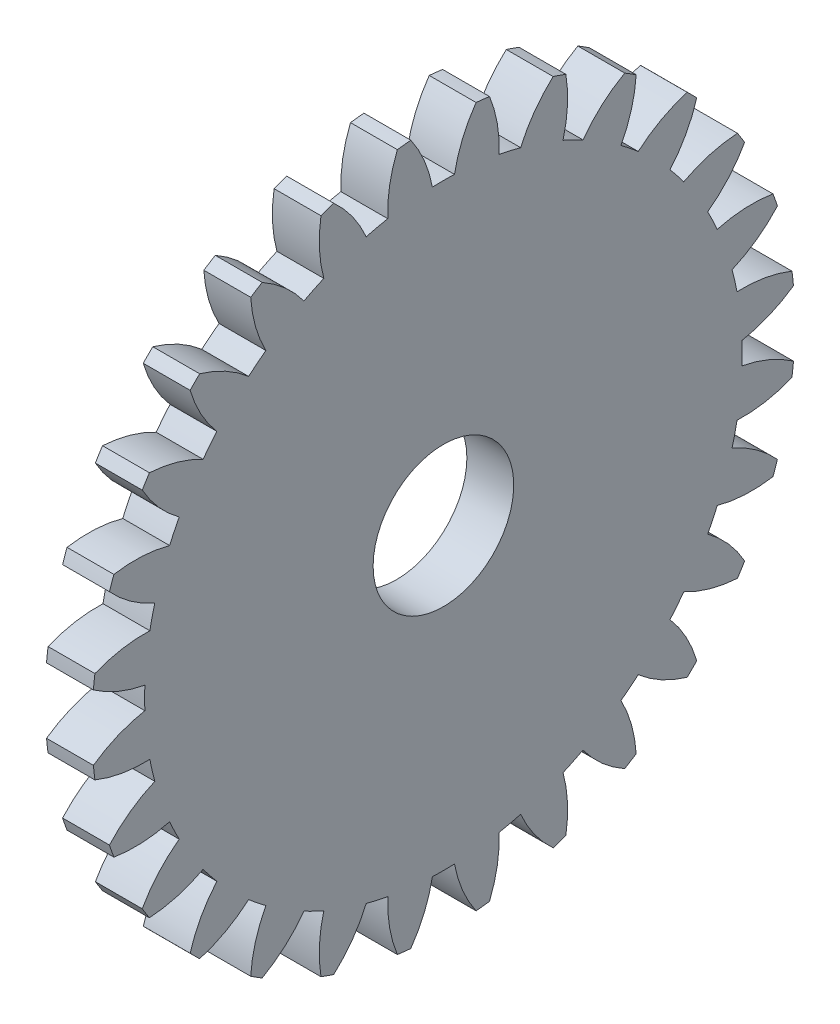
SolidWorks part; units mm, degrees
ref_plane "Plane1" through (0, 0, 0) normal (0, 0, 1) x (1, 0, 0)
ref_plane "Plane2" through (0, 0, 0) normal (0, 1, 0) x (1, 0, 0)
ref_plane "Plane3" through (0, 0, 0) normal (1, 0, 0) x (0, 0, -1)
sketch "HoldingSke" plane through (0, 0, 0) normal (0, 1, 0) x (1, 0, 0)
  line L0 (0, 0) -> (0.8829, -0.4695)
  line L1 (-15, 0) -> (100, 0) construction
  line L2 (0, 0) -> (-2.1039, 2.3779)
  line L3 (0, 0) -> (-11.863, 4.5341)
  line L4 (0, 0) -> (7.6251, 4.0544)
  line L5 (0, 0) -> (-46.8476, -17.4728)
  line L6 (0, 0) -> (-1.6579, -1.1186)
  line L7 (-2.1039, 2.3779) -> (8.6586, 51.2059)
  line L8 (-76.2, 54.61) -> (-75.2, 54.61)
  line L9 (-71.009, 38.7566) -> (-53.1078, 45.2721)
  line L10 (-76.2, 71.12) -> (104.1128, 71.12)
  line L11 (0, 0) -> (-2, 0)
  line L12 (-76.2, 101.6) -> (-76.162, 101.6)
  line L13 (24.9733, 27.94) -> (52.9518, 28.4284)
  line L14 (24.9733, 27.94) -> (24.9743, 27.94)
  line L15 (24.9733, 27.94) -> (100.4006, 29.5858)
  line L16 (-63.627, -1) -> (-12.827, -1)
  circle A0 centre (0, 0) radius 3
  circle A1 centre (0, 0) radius 12.749
  circle A2 centre (0, 0) radius 37.5
  circle A3 centre (0, 0) radius 3
  dimension "MHD" = 25.498
  dimension "Hub_dia" = 75
  dimension "Bore" = 6
  dimension "MBD" = 6
  dimension "Num_teeth" = 28
  dimension "Pitch_radius" = 180.3128
  dimension "Pitch" = 1
  dimension "Width" = 2
  dimension "Overall_len" = 50
  dimension "Show_teeth" = 28
  dimension "Thickness" = 2
  dimension "OAL" = 50.0001
  dimension "T_dim" = 1
  dimension "Ap" = 20
  dimension "H" = 19.05
  dimension "Backlash" = 0.038
  dimension "Addendum_fac" = 1
  dimension "Dedendum_fac" = 1.25
  dimension "Clearance_fac" = 0.25
  dimension "Dedendum_add" = 0.001
  dimension "Module" = 1
sketch "BasProSke" plane through (0, 0, 0) normal (0, 1, 0) x (1, 0, 0)
  line L0 (-10, 0) -> (60, 0) construction
  line L1 (0, 0) -> (0, 15)
  line L2 (0, 0) -> (2, 0)
  line L3 (2, 0) -> (2, 15)
  line L4 (2, 15) -> (0, 15)
  dimension "Diameter" = 30
  dimension "Thickness" = 2
revolve "Base-Revolve" add sketch "BasProSke" angle 360 about L0
sketch "TooCutSke" plane through (0, 0, 0) normal (1, 0, 0) x (0, 0, -1)
  line L1 (0, 0) -> (0, 107) construction
  line L2 (0, 0) -> (-0.8515, 13.9741) construction
  line L3 (0, 0) -> (-3.1309, 27.7873) construction
  line L4 (-0.8515, 13.9741) -> (-1.5654, 13.8936) construction
  arc A0 (0.4713, 12.7403) -> (-0.4713, 12.7403) centre (0, 0) ccw
  arc A1 (1.4098, 14.9591) -> (-1.4098, 14.9591) centre (0, 0) ccw
  circle A2 centre (0, 0) radius 14 construction
  circle A3 centre (0, 0) radius 13.1557 construction
  arc A4 (-0.4713, 12.7403) -> (-1.4098, 14.9591) centre (-5.9775, 11.7193) ccw
  arc A5 (1.4098, 14.9591) -> (0.4713, 12.7403) centre (5.9775, 11.7193) ccw
  dimension "Root_dia" = 25.498
  dimension "Overcut_dia" = 30.0508
  dimension "Pitch_dia" = 28
  dimension "Base_dia" = 26.3114
  dimension "Flank_rad" = 5.6
  dimension "Half_ang" = 6.429
  dimension "Half_CT" = 0.7185
extrude "ToothCut" cut sketch "TooCutSke" along normal through all
fillet "Breaks" [suppressed] radius 0.02
fillet "RootFillets" [suppressed] radius 0.251
pattern_circular "TeethCuts" count 28 every 12.857 about axis through (-10, 0, 0) along (1, 0, 0) of "ToothCut", "RootFillets", "Breaks"
sketch "HubNeaOneSke" plane through (0, 0, 0) normal (-1, 0, 0) x (0, 0, 1)
  circle A0 centre (0, 0) radius 12.749
  dimension "Diameter" = 25.498
extrude "HubNearOne" [suppressed] add sketch "HubNeaOneSke" along normal blind 48.0001
sketch "HubNeaBotSke" plane through (0, 0, 0) normal (-1, 0, 0) x (0, 0, 1)
  circle A0 centre (0, 0) radius 12.749
  dimension "Diameter" = 25.498
extrude "HubNearBoth" [suppressed] add sketch "HubNeaBotSke" along normal blind 24
ref_plane "FarPln" through (2, 0, 0) normal (1, 0, 0) x (0, 0, -1)
sketch "HubFarSke" plane through (2, 0, 0) normal (1, 0, 0) x (0, 0, -1)
  circle A0 centre (0, 0) radius 12.749
  dimension "Diameter" = 25.498
extrude "HubFar" [suppressed] add sketch "HubFarSke" along normal blind 24
sketch "BorSke" plane through (0, 0, 0) normal (1, 0, 0) x (0, 0, -1)
  circle A0 centre (0, 0) radius 3
  dimension "Diameter" = 6
extrude "Bore" cut sketch "BorSke" along normal mid plane 100.0001
sketch "KeySke" plane through (0, 0, 0) normal (1, 0, 0) x (0, 0, -1)
  line L0 (-1, 0) -> (-1, 4)
  line L1 (-1, 4) -> (1, 4)
  line L2 (1, 4) -> (1, 0)
  line L3 (0, 0) -> (0, 34) construction
  line L4 (-1, 0) -> (1, 0)
  dimension "Offset" = 4
  dimension "Width" = 2
extrude "Keyway" [suppressed] cut sketch "KeySke" along normal mid plane 100.0001
pattern_circular "Keyway2" [suppressed] count 2 every 90 about axis through (-10, 0, 0) along (1, 0, 0)
equation "' \"Module@HoldingSke\" = 6.35"
equation "' \"Num_teeth@HoldingSke\" = 12"
equation "' \"Ap@HoldingSke\" =  20"
equation "' \"Width@HoldingSke\" = 0.5 * 25.4"
equation "' \"Hub_dia@HoldingSke\"= 1 * 25.4"
equation "' \"Overall_len@HoldingSke\" = 1.0 * 25.4"
equation "' \"Bore@HoldingSke\" = 0.75 * 25.4"
equation "' \"T_dim@HoldingSke\" = 0.1 * 25.4"
equation "' \"Width@KeySke\" = 0.25 * 25.4"
equation "' \"Show_teeth@HoldingSke\" = 13"
equation "' \"Backlash@HoldingSke\" = 0.009 * 25.4"
equation "' \"Addendum_fac@HoldingSke\" = 1.0"
equation "' \"Dedendum_fac@HoldingSke\" = 1.25"
equation "' \"Dedendum_add@HoldingSke\" = 0.00005 * 25.4"
equation "' \"Clearance_fac@HoldingSke\" = 0.25"
equation "\"Pitch@HoldingSke\" = 1 / \"Module@HoldingSke\""
equation "\"Overcut_dia@TooCutSke\" = (\"Num_teeth@HoldingSke\" + 2 * \"Addendum_fac@HoldingSke\") / \"Pitch@HoldingSke\" + 0.002 * 25.4"
equation "\"Pitch_dia@TooCutSke\" = \"Num_teeth@HoldingSke\" / \"Pitch@HoldingSke\""
equation "\"Base_dia@TooCutSke\" = \"Num_teeth@HoldingSke\" / \"Pitch@HoldingSke\" * cos((\"Ap@HoldingSke\"  * 3.14159265 / 180))"
equation "\"Root_dia@TooCutSke\" = (\"Num_teeth@HoldingSke\" + 2) / \"Pitch@HoldingSke\" - 2 * (\"Addendum_fac@HoldingSke\" + \"Dedendum_fac@HoldingSke\") / \"Pitch@HoldingSke\" - \"Dedendum_add@HoldingSke\" * 2"
equation "\"Half_ang@TooCutSke\" = 180 / \"Num_teeth@HoldingSke\""
equation "\"Half_CT@TooCutSke\" = \"Num_teeth@HoldingSke\" / \"Pitch@HoldingSke\" * sin((3.14159265 / 2 / \"Num_teeth@HoldingSke\")) / 2 - 7 * \"Backlash@HoldingSke\" / 4"
equation "\"Flank_rad@TooCutSke\" = \"Num_teeth@HoldingSke\" / \"Pitch@HoldingSke\" / 5"
equation "\"Radius@RootFillets\" = \"Clearance_fac@HoldingSke\" / \"Pitch@HoldingSke\" + \"Dedendum_add@HoldingSke\""
equation "\"Break_rad@Breaks\" = 0.02 / \"Pitch@HoldingSke\""
equation "\"Thickness@HoldingSke\" = \"Width@HoldingSke\""
equation "\"OAL@HoldingSke\" = \"Thickness@HoldingSke\""
equation "\"MHD@HoldingSke\" = (\"Num_teeth@HoldingSke\" + 2) / \"Pitch@HoldingSke\" - 2 * (\"Addendum_fac@HoldingSke\" + \"Dedendum_fac@HoldingSke\")  / \"Pitch@HoldingSke\" - \"Dedendum_add@HoldingSke\" * 2"
equation "\"MBD@HoldingSke\" = (\"Num_teeth@HoldingSke\" + 2) / \"Pitch@HoldingSke\" - 2 * (\"Addendum_fac@HoldingSke\" + \"Dedendum_fac@HoldingSke\")  / \"Pitch@HoldingSke\" - \"Dedendum_add@HoldingSke\" * 2 - 0.002 * 25.4"
equation "\"MHD@HoldingSke\" = ((sgn( \"MHD@HoldingSke\" - \"Hub_dia@HoldingSke\" )-1)*( \"MHD@HoldingSke\" - \"Hub_dia@HoldingSke\" ))/-2+ \"Hub_dia@HoldingSke\""
equation "\"MBD@HoldingSke\" = ((sgn( \"MBD@HoldingSke\" - \"Bore@HoldingSke\" )-1)*( \"MBD@HoldingSke\" - \"Bore@HoldingSke\" ))/-2+ \"Bore@HoldingSke\""
equation "\"OAL@HoldingSke\" = ((sgn( \"OAL@HoldingSke\" - \"Overall_len@HoldingSke\" )+1)*( \"OAL@HoldingSke\" - \"Overall_len@HoldingSke\" ))/2 + \"Overall_len@HoldingSke\" + 0.000002 * 25.4"
equation "\"Num_teeth@TeethCuts\" = int( \"Show_teeth@HoldingSke\" ) + 1"
equation "\"Num_teeth@TeethCuts\" = ((sgn( \"Num_teeth@TeethCuts\" - \"Num_teeth@HoldingSke\" )-1)*( \"Num_teeth@TeethCuts\" - \"Num_teeth@HoldingSke\" ))/-2+ \"Num_teeth@HoldingSke\""
equation "\"Num_teeth@TeethCuts\" = ((sgn( \"Num_teeth@TeethCuts\" - 2.0)+1)*( \"Num_teeth@TeethCuts\" - 2.0))/2 +2.0"
equation "\"Angle@TeethCuts\" = 360.0 / \"Num_teeth@HoldingSke\""
equation "\"Diameter@BasProSke\" = (\"Num_teeth@HoldingSke\" + 2 * \"Addendum_fac@HoldingSke\") / \"Pitch@HoldingSke\""
equation "\"Thickness@BasProSke\"  = \"Thickness@HoldingSke\""
equation "' \"Fillet_rad@BasProSke\" =  \"Thickness@HoldingSke\" * 0.05"
equation "\"MHD@HoldingSke\" = ((sgn( \"MHD@HoldingSke\" - \"Root_dia@TooCutSke\" )-1)*( \"MHD@HoldingSke\" - \"Root_dia@TooCutSke\" ))/-2+ \"Root_dia@TooCutSke\""
equation "\"Diameter@HubNeaOneSke\" = \"MHD@HoldingSke\""
equation "\"Length@HubNearOne\" = \"OAL@HoldingSke\" - \"Thickness@BasProSke\""
equation "\"Diameter@HubNeaBotSke\" = \"MHD@HoldingSke\""
equation "\"Length@HubNearBoth\" = ( \"OAL@HoldingSke\" - \"Thickness@BasProSke\" ) / 2.0"
equation "\"Thickness@FarPln\" = \"Thickness@BasProSke\""
equation "\"Diameter@HubFarSke\" = \"MHD@HoldingSke\""
equation "\"Length@HubFar\" = ( \"OAL@HoldingSke\" - \"Thickness@BasProSke\" ) / 2.0"
equation "\"Diameter@BorSke\" = \"MBD@HoldingSke\""
equation "\"D1@Bore\" = \"OAL@HoldingSke\" * 2.0"
equation "\"D1@Keyway\" = \"OAL@HoldingSke\" * 2.0"
equation "\"Offset@KeySke\" = \"T_dim@HoldingSke\" + \"MBD@HoldingSke\" / 2.0"
